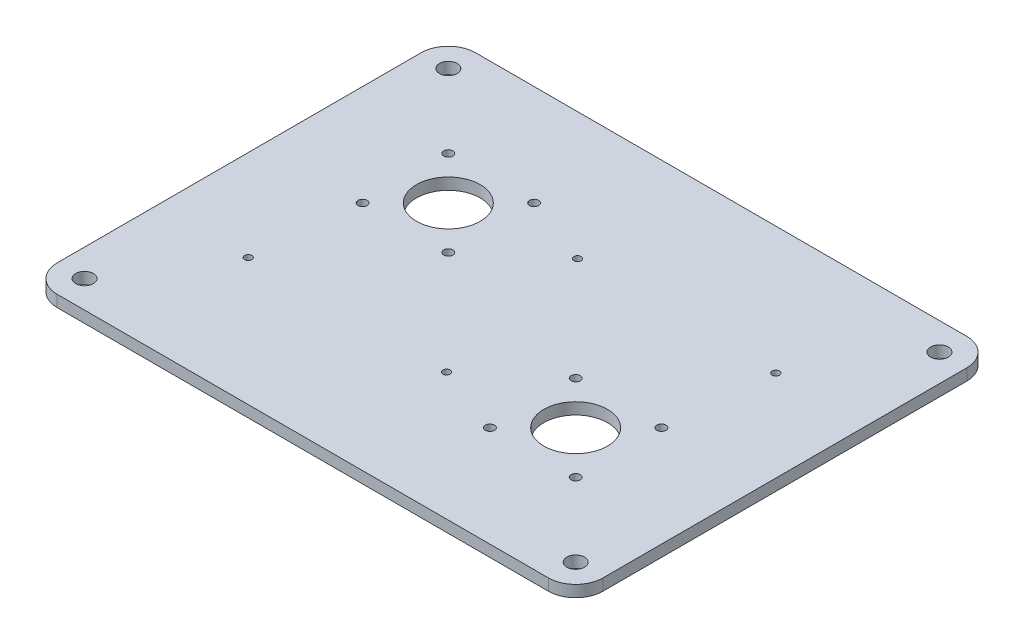
SolidWorks part; units mm, degrees
ref_plane "Front Plane" through (0, 0, 0) normal (0, 0, 1) x (1, 0, 0)
ref_plane "Top Plane" through (0, 0, 0) normal (0, 1, 0) x (1, 0, 0)
ref_plane "Right Plane" through (0, 0, 0) normal (1, 0, 0) x (0, 0, -1)
sketch "Sketch1" plane through (0, 0, 0) normal (0, 1, 0) x (1, 0, 0)
  line L0 (-98.6514, 56.4216) -> (-38.6514, 116.4216) construction
  line L1 (-132.6514, 165.4216) -> (137.3486, 165.4216)
  line L2 (-147.6514, 150.4216) -> (-147.6514, -49.5784)
  line L3 (-132.6514, -64.5784) -> (137.3486, -64.5784)
  line L4 (152.3486, 150.4216) -> (152.3486, -49.5784)
  line L5 (-98.6514, 116.4216) -> (-38.6514, 116.4216) construction
  line L6 (-98.6514, 116.4216) -> (-98.6514, 56.4216) construction
  line L7 (-98.6514, 56.4216) -> (-38.6514, 56.4216) construction
  line L8 (-38.6514, 116.4216) -> (-38.6514, 56.4216) construction
  line L9 (43.3486, 44.4216) -> (103.3486, 44.4216) construction
  line L10 (43.3486, 44.4216) -> (43.3486, -15.5784) construction
  line L11 (43.3486, -15.5784) -> (103.3486, -15.5784) construction
  line L12 (103.3486, 44.4216) -> (103.3486, -15.5784) construction
  line L13 (-147.6514, 50.4216) -> (-247.1624, 50.4216) construction
  line L14 (43.3486, -15.5784) -> (103.3486, 44.4216) construction
  line L15 (-239.9356, -24.5784) -> (381.8145, -24.5784) construction
  line L16 (-239.9356, -24.5784) -> (-239.9356, -64.5784) construction
  line L17 (-239.9356, -64.5784) -> (381.8145, -64.5784) construction
  line L18 (381.8145, -24.5784) -> (381.8145, -64.5784) construction
  line L19 (-92.2214, 62.8516) -> (-45.0814, 62.8516) construction
  line L20 (-92.2214, 62.8516) -> (-92.2214, 109.9916) construction
  line L21 (-92.2214, 109.9916) -> (-45.0814, 109.9916) construction
  line L22 (-45.0814, 62.8516) -> (-45.0814, 109.9916) construction
  line L23 (-92.2214, 62.8516) -> (-45.0814, 109.9916) construction
  line L24 (-92.2214, 109.9916) -> (-45.0814, 62.8516) construction
  line L25 (49.7786, -9.1484) -> (96.9186, -9.1484) construction
  line L26 (49.7786, -9.1484) -> (49.7786, 37.9916) construction
  line L27 (49.7786, 37.9916) -> (96.9186, 37.9916) construction
  line L28 (96.9186, -9.1484) -> (96.9186, 37.9916) construction
  line L29 (49.7786, -9.1484) -> (96.9186, 37.9916) construction
  line L30 (49.7786, 37.9916) -> (96.9186, -9.1484) construction
  line L31 (-239.9356, 165.4216) -> (381.8145, 165.4216) construction
  line L32 (-132.6514, 165.4216) -> (137.3486, 165.4216)
  circle A2 centre (-68.6514, 86.4216) radius 76.85 construction
  circle A3 centre (73.3486, 14.4216) radius 76.85 construction
  circle A4 centre (-132.6514, 150.4216) radius 15 construction
  circle A5 centre (-132.6514, 150.4216) radius 4.85
  arc A6 (152.3486, 150.4216) -> (137.3486, 165.4216) centre (137.3486, 150.4216) ccw
  arc A7 (152.3486, -49.5784) -> (137.3486, -64.5784) centre (137.3486, -49.5784) cw
  arc A8 (-147.6514, -49.5784) -> (-132.6514, -64.5784) centre (-132.6514, -49.5784) ccw
  arc A9 (-147.6514, 150.4216) -> (-132.6514, 165.4216) centre (-132.6514, 150.4216) cw
  circle A10 centre (137.3486, -49.5784) radius 15 construction
  circle A11 centre (137.3486, -49.5784) radius 4.85
  circle A12 centre (-45.0814, 109.9916) radius 2.5
  circle A13 centre (-45.0814, 62.8516) radius 2.5
  circle A14 centre (-92.2214, 62.8516) radius 2.5
  circle A15 centre (-92.2214, 109.9916) radius 2.5
  circle A16 centre (49.7786, 37.9916) radius 2.5
  circle A17 centre (96.9186, 37.9916) radius 2.5
  circle A18 centre (96.9186, -9.1484) radius 2.5
  circle A19 centre (49.7786, -9.1484) radius 2.5
  circle A20 centre (137.3486, 150.4216) radius 15 construction
  circle A21 centre (137.3486, 150.4216) radius 4.85
  arc A22 (152.3486, 150.4216) -> (137.3486, 165.4216) centre (137.3486, 150.4216) ccw
  circle A23 centre (-132.6514, -49.5784) radius 15 construction
  arc A24 (-147.6514, -49.5784) -> (-132.6514, -64.5784) centre (-132.6514, -49.5784) ccw
  circle A25 centre (-132.6514, -49.5784) radius 4.85
  circle A26 centre (-68.6514, 86.4216) radius 17.5
  circle A27 centre (73.3486, 14.4216) radius 17.5
  point P12 (73.3486, 14.4216)
  dimension "D8" = 153.7
  dimension "D10" = 9.7
  dimension "D13" = 15
  dimension "D14" = 9.7
  dimension "D18" = 5
  dimension "D9" = 35
  dimension "D3" = 60
  dimension "D2" = 230
  dimension "D6" = 300
  dimension "D7" = 40
  dimension "D15" = 49
  dimension "D16" = 49
  dimension "D17" = 49
  dimension "D5" = 49
  dimension "D4" = 47.14
extrude "Boss-Extrude1" add sketch "Sketch1" along normal blind 6.35
sketch "Sketch5" plane through (0, 0, 0) normal (0, -1, 0) x (1, 0, 0)
  line L0 (-97.6514, -5.4216) -> (11.3486, -5.4216) construction
  line L1 (-147.6514, -150.4216) -> (-147.6514, 49.5784) construction
  line L2 (152.3486, -50.4216) -> (-147.6514, -50.4216) construction
  line L3 (152.3486, -150.4216) -> (152.3486, 49.5784) construction
  line L4 (-6.6514, -95.4216) -> (102.3486, -95.4216) construction
  line L5 (-132.6514, 64.5784) -> (137.3486, 64.5784) construction
  line L6 (-132.6514, -165.4216) -> (137.3486, -165.4216) construction
  circle A0 centre (-97.6514, -5.4216) radius 2
  circle A1 centre (11.3486, -5.4216) radius 2
  circle A4 centre (-6.6514, -95.4216) radius 2
  circle A5 centre (102.3486, -95.4216) radius 2
  point P10 (2.3486, -50.4216)
  dimension "D1" = 4
  dimension "D3" = 4
  dimension "D2" = 109
  dimension "D4" = 109
  dimension "D5" = 70
  dimension "D6" = 50
  dimension "D7" = 50
  dimension "D8" = 70
extrude "Cut-Extrude2" cut sketch "Sketch5" against normal blind 10
equation "\"D16@Sketch1\"=\"D15@Sketch1\""
equation "\"D17@Sketch1\"=\"D15@Sketch1\""
equation "\"D5@Sketch1\"=\"D15@Sketch1\""
equation "\"D14@Sketch1\"=\"D10@Sketch1\""
equation "\"D7@Sketch5\"=\"D6@Sketch5\""
equation "\"D8@Sketch5\"=\"D5@Sketch5\""
